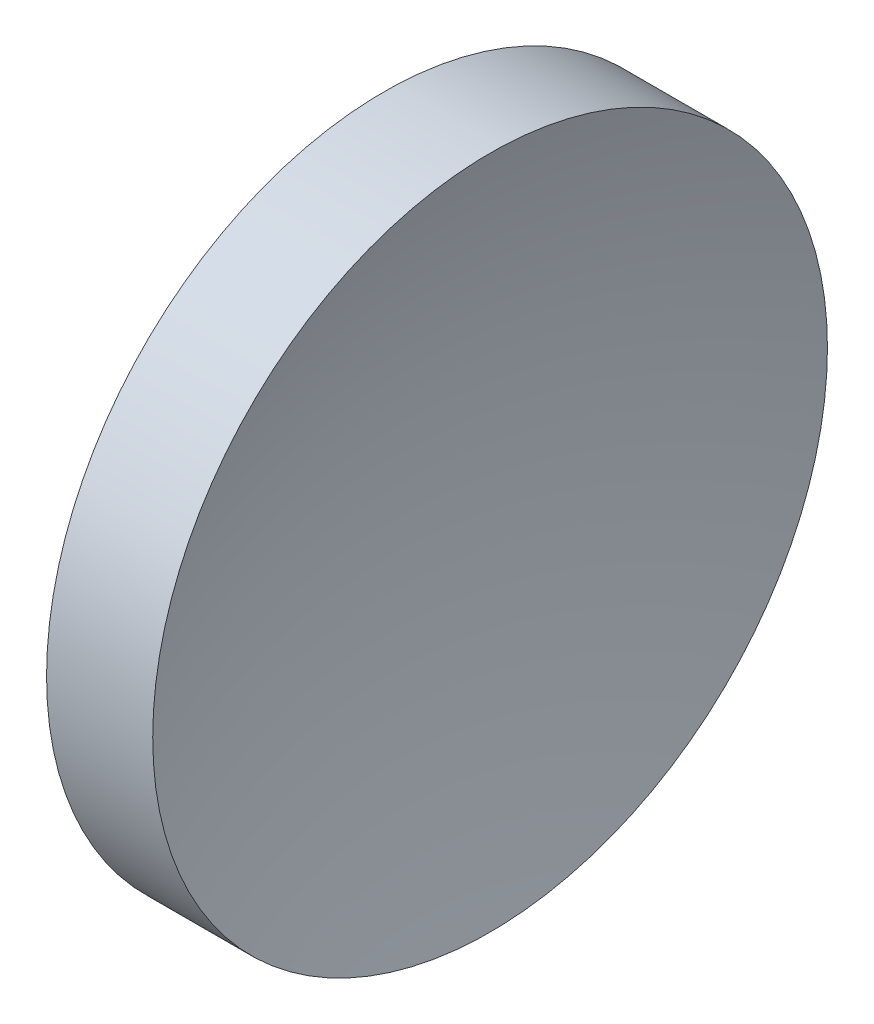
SolidWorks part; units mm, degrees
ref_plane "前视基准面" through (0, 0, 0) normal (0, 0, 1) x (1, 0, 0)
ref_plane "上视基准面" through (0, 0, 0) normal (0, 1, 0) x (1, 0, 0)
ref_plane "右视基准面" through (0, 0, 0) normal (1, 0, 0) x (0, 0, -1)
sketch "草图1" plane through (0, 0, 0) normal (0, 0, 1) x (1, 0, 0)
  line L0 (56.1009, 32.6108) -> (68.2773, 32.6108) construction
  line L1 (57.5323, 32.6108) -> (57.5323, 45.1108)
  line L2 (57.5323, 45.1108) -> (61.4657, 45.1108)
  line L3 (59.5323, 32.6108) -> (57.5323, 32.6108)
  arc A0 (61.4657, 45.1108) -> (59.5323, 32.6108) centre (100.8323, 32.6224) ccw
revolve "旋转1" add sketch "草图1" angle 360 about L0
